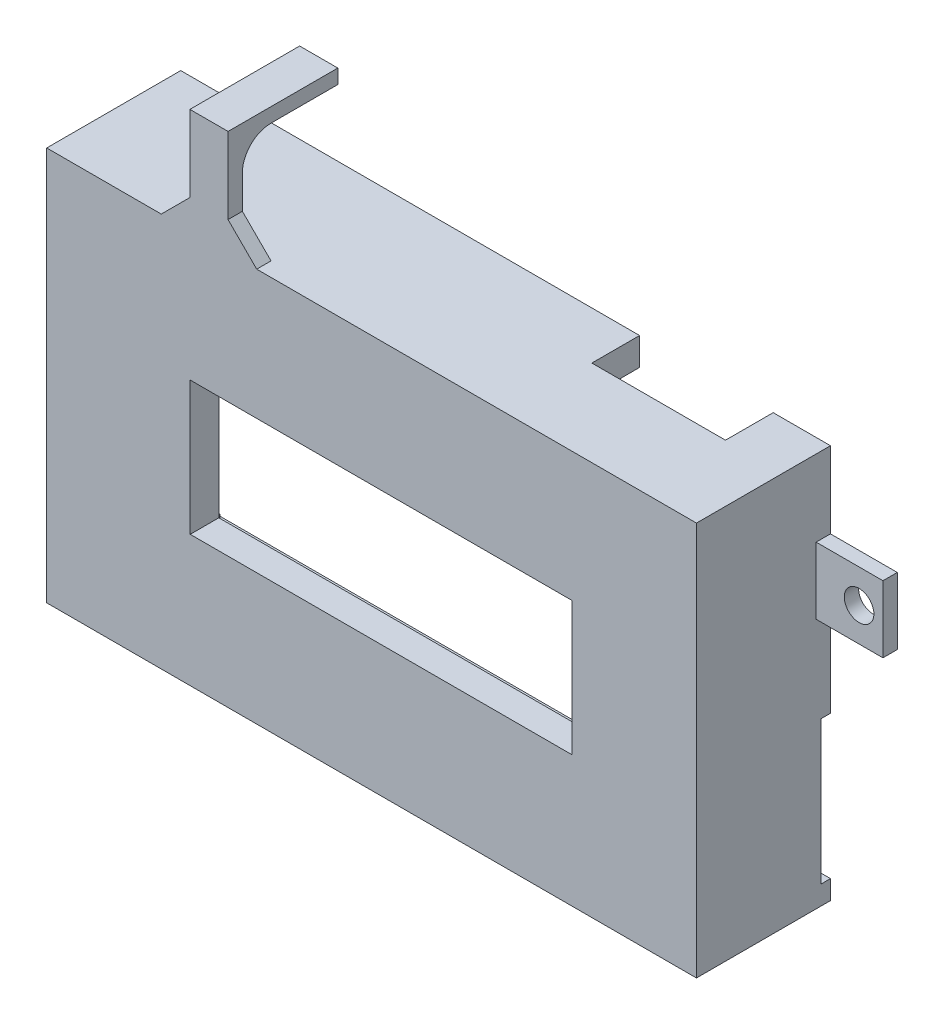
SolidWorks part; units mm, degrees
ref_plane "前视基准面" through (0, 0, 0) normal (0, 0, 1) x (1, 0, 0)
ref_plane "上视基准面" through (0, 0, 0) normal (0, 1, 0) x (1, 0, 0)
ref_plane "右视基准面" through (0, 0, 0) normal (1, 0, 0) x (0, 0, -1)
other "Configuration Table"
sketch "草图1" plane through (0, 0, 0) normal (0, 0, 1) x (1, 0, 0)
  line L0 (0, 0) -> (0, 12) construction
  line L1 (0, 0) -> (38, 0) construction
  line L2 (-1, -1) -> (39, -1)
  line L3 (-1, -1) -> (-1, 13)
  line L4 (-1, 13) -> (39, 13)
  line L5 (39, -1) -> (39, 13)
  line L6 (-16.0353, -14.7373) -> (52.0424, -14.7373)
  line L7 (-16.0353, -14.7373) -> (-16.0353, 26.5433)
  line L8 (-16.0353, 26.5433) -> (52.0424, 26.5433)
  line L9 (52.0424, -14.7373) -> (52.0424, 26.5433)
  line L10 (0, 12) -> (38, 12) construction
  line L11 (38, 0) -> (38, 12) construction
  line L12 (49.0424, 23.5433) -> (-13.0353, 23.5433) construction
  line L13 (-13.0353, 23.5433) -> (-13.0353, -11.7373) construction
  line L15 (-13.0353, -11.7373) -> (49.0424, -11.7373) construction
  line L16 (49.0424, -11.7373) -> (49.0424, 23.5433) construction
  dimension "D1" = 1
  dimension "D2" = 1
  dimension "D3" = 1
  dimension "D4" = 1
  dimension "D5" = 3
  dimension "D6" = 3
  dimension "D7" = 3
  dimension "D8" = 3
extrude "凸台-拉伸1" add sketch "草图1" against normal blind 3
sketch "草图2" plane through (0, 0, -3) normal (0, 0, -1) x (-1, 0, 0)
  line L0 (13.0353, 23.5433) -> (13.0353, -11.7373) construction
  line L1 (13.1353, 23.6433) -> (-49.5424, 23.6433)
  line L2 (13.1353, 23.6433) -> (13.1353, -11.8373)
  line L3 (13.1353, -11.8373) -> (-49.5424, -11.8373)
  line L4 (-49.5424, 23.6433) -> (-49.5424, -11.8373)
  line L5 (-49.0424, 23.5433) -> (13.0353, 23.5433) construction
  line L6 (13.0353, -11.7373) -> (-49.0424, -11.7373) construction
  line L7 (-49.0424, -11.7373) -> (-49.0424, 23.5433) construction
  line L9 (-52.0424, 26.5433) -> (16.0353, 26.5433)
  line L10 (-52.0424, 26.5433) -> (-52.0424, -14.7373)
  line L11 (-52.0424, -14.7373) -> (16.0353, -14.7373)
  line L12 (16.0353, 26.5433) -> (16.0353, -14.7373)
  dimension "D1" = 0.1
  dimension "D2" = 0.1
  dimension "D3" = 0.1
  dimension "D4" = 0.5
extrude "凸台-拉伸2" add sketch "草图2" along normal up to surface (11.0401 mm away)
sketch "草图3" plane through (-16.0353, 0, 0) normal (-1, 0, 0) x (0, 0, 1)
  line L0 (-14.0401, 26.5433) -> (-14.0401, -14.7373) construction
  line L1 (-14.0401, 0.2627) -> (-7, 0.2627)
  line L2 (-14.0401, 0.2627) -> (-14.0401, 11.5433)
  line L3 (-14.0401, 11.5433) -> (-7, 11.5433)
  line L4 (-7, 0.2627) -> (-7, 11.5433)
  line L5 (-14.0401, -14.7373) -> (0, -14.7373) construction
  line L6 (-14.0401, 26.5433) -> (0, 26.5433) construction
  line L7 (0, 26.5433) -> (0, -14.7373) construction
  dimension "D1" = 15
  dimension "D2" = 15
  dimension "D3" = 7
extrude "切除-拉伸1" cut sketch "草图3" against normal up to surface (2.9 mm away) up to face at (-13.1353, 5.903, -8.52)
sketch "草图4" plane through (0, 23.6433, 0) normal (0, -1, 0) x (1, 0, 0)
  line L0 (49.5424, -14.0401) -> (49.5424, -3) construction
  line L1 (49.5424, -12.2401) -> (46.5424, -12.2401)
  line L2 (49.5424, -12.2401) -> (49.5424, -10.4401)
  line L3 (49.5424, -10.4401) -> (46.5424, -10.4401)
  line L4 (46.5424, -12.2401) -> (46.5424, -10.4401)
  line L5 (49.5424, -14.0401) -> (-13.1353, -14.0401) construction
  dimension "D1" = 1.8
  dimension "D2" = 1.8
  dimension "D3" = 3
extrude "凸台-拉伸3" add sketch "草图4" along normal blind 3
sketch "草图5" plane through (0, -11.8373, 0) normal (0, 1, 0) x (1, 0, 0)
  line L0 (49.5424, 14.0401) -> (49.5424, 3) construction
  line L1 (49.5424, 12.2401) -> (46.5424, 12.2401)
  line L2 (49.5424, 12.2401) -> (49.5424, 10.4401)
  line L3 (49.5424, 10.4401) -> (46.5424, 10.4401)
  line L4 (46.5424, 12.2401) -> (46.5424, 10.4401)
  line L5 (-13.1353, 14.0401) -> (49.5424, 14.0401) construction
  dimension "D1" = 1.8
  dimension "D2" = 1.8
  dimension "D3" = 3
extrude "凸台-拉伸4" add sketch "草图5" along normal blind 3
sketch "草图6" plane through (0, 23.6433, 0) normal (0, -1, 0) x (1, 0, 0)
  line L0 (-13.1353, -14.0401) -> (-13.1353, -3) construction
  line L1 (-13.1353, -12.2401) -> (-10.1353, -12.2401)
  line L2 (-13.1353, -12.2401) -> (-13.1353, -10.4401)
  line L3 (-13.1353, -10.4401) -> (-10.1353, -10.4401)
  line L4 (-10.1353, -12.2401) -> (-10.1353, -10.4401)
  line L5 (49.5424, -14.0401) -> (-13.1353, -14.0401) construction
  dimension "D1" = 1.8
  dimension "D2" = 1.8
  dimension "D3" = 3
extrude "凸台-拉伸5" add sketch "草图6" along normal blind 2
sketch "草图7" plane through (0, -11.8373, 0) normal (0, 1, 0) x (1, 0, 0)
  line L1 (-13.1353, 14.0401) -> (-13.1353, 3) construction
  line L2 (-13.1353, 12.2401) -> (-10.1353, 12.2401)
  line L3 (-13.1353, 12.2401) -> (-13.1353, 10.4401)
  line L4 (-13.1353, 10.4401) -> (-10.1353, 10.4401)
  line L5 (-10.1353, 12.2401) -> (-10.1353, 10.4401)
  line L6 (-13.1353, 14.0401) -> (49.5424, 14.0401) construction
  dimension "D1" = 1.8
  dimension "D2" = 1.8
  dimension "D3" = 3
extrude "凸台-拉伸6" add sketch "草图7" along normal blind 2
sketch "草图8" plane through (0, 26.5433, 0) normal (0, 1, 0) x (1, 0, 0)
  line L0 (52.0424, 14.0401) -> (-16.0353, 14.0401) construction
  line L1 (32.0424, 14.0401) -> (46.0424, 14.0401)
  line L2 (32.0424, 14.0401) -> (32.0424, 9.0401)
  line L3 (32.0424, 9.0401) -> (46.0424, 9.0401)
  line L4 (46.0424, 14.0401) -> (46.0424, 9.0401)
  line L5 (52.0424, 14.0401) -> (52.0424, 0) construction
  dimension "D1" = 6
  dimension "D2" = 14
  dimension "D3" = 5
extrude "切除-拉伸2" cut sketch "草图8" against normal up to surface (2.9 mm away) up to face at (18.2035, 23.6433, -10.4)
sketch "草图9" plane through (52.0424, 0, 0) normal (1, 0, 0) x (0, 0, -1)
  line L1 (14.0401, -14.7373) -> (14.0401, 26.5433) construction
  line L2 (14.0401, -12.7373) -> (13.0401, -12.7373)
  line L3 (14.0401, -12.7373) -> (14.0401, 2.2627)
  line L4 (14.0401, 2.2627) -> (13.0401, 2.2627)
  line L5 (13.0401, -12.7373) -> (13.0401, 2.2627)
  line L6 (14.0401, -12.7373) -> (22.0401, -12.7373) construction
  line L7 (22.0401, 2.2627) -> (14.0401, 2.2627) construction
  dimension "D1" = 0
  dimension "D2" = 1
extrude "切除-拉伸3" cut sketch "草图9" against normal blind 1
sketch "草图10" plane through (52.0424, 0, 0) normal (1, 0, 0) x (0, 0, -1)
  line L1 (14.0401, 2.2627) -> (14.0401, 26.5433) construction
  line L2 (14.0401, 11.5433) -> (12.5401, 11.5433)
  line L3 (14.0401, 11.5433) -> (14.0401, 18.5433)
  line L4 (14.0401, 18.5433) -> (12.5401, 18.5433)
  line L5 (12.5401, 11.5433) -> (12.5401, 18.5433)
  line L6 (14.0401, 26.5433) -> (0, 26.5433) construction
  dimension "D1" = 8
  dimension "D2" = 7
  dimension "D3" = 1.5
extrude "凸台-拉伸7" add sketch "草图10" along normal blind 7
sketch "草图13" plane through (0, 0, -12.5401) normal (0, 0, 1) x (1, 0, 0)
  line L0 (59.0424, 11.5433) -> (52.0424, 11.5433) construction
  line L1 (59.0424, 18.5433) -> (59.0424, 11.5433) construction
  circle A0 centre (56.5424, 15.0433) radius 1.55
  dimension "D3" = 3.1
  dimension "D1" = 3.5
  dimension "D2" = 2.5
extrude "切除-拉伸6" cut sketch "草图13" against normal through all
sketch "草图14" plane through (0, 26.5433, 0) normal (0, 1, 0) x (1, 0, 0)
  line L0 (52.0424, 0) -> (-16.0353, 0) construction
  line L1 (2.9647, 0) -> (-1.0353, 0)
  line L2 (2.9647, 0) -> (2.9647, 1.5)
  line L3 (2.9647, 1.5) -> (-1.0353, 1.5)
  line L4 (-1.0353, 0) -> (-1.0353, 1.5)
  line L5 (-16.0353, 14.0401) -> (-16.0353, 0) construction
  dimension "D1" = 15
  dimension "D2" = 4
  dimension "D3" = 1.5
extrude "凸台-拉伸8" add sketch "草图14" along normal blind 11
sketch "草图15" plane through (0, 0, -1.5) normal (0, 0, -1) x (-1, 0, 0)
  line L0 (1.0353, 37.5433) -> (1.0353, 26.5433) construction
  line L1 (-2.9647, 37.5433) -> (1.0353, 37.5433)
  line L2 (-2.9647, 37.5433) -> (-2.9647, 36.0433)
  line L3 (-2.9647, 36.0433) -> (1.0353, 36.0433)
  line L4 (1.0353, 37.5433) -> (1.0353, 36.0433)
  dimension "D1" = 1.5
extrude "凸台-拉伸9" add sketch "草图15" along normal blind 10
chamfer "倒角1" distance 3 angle 45 2 edges at (2.9647, 26.5433, -0.75) (-1.0353, 26.5433, -0.75)
fillet "圆角2" radius 3 1 edges at (0.9647, 36.0433, -1.5)
sketch "草图16" plane through (0, -14.7373, 0) normal (0, -1, 0) x (1, 0, 0)
  line L0 (-16.0353, -14.0401) -> (52.0424, -14.0401) construction
  line L1 (13.9647, -14.0401) -> (20.9647, -14.0401)
  line L2 (13.9647, -14.0401) -> (13.9647, -12.5401)
  line L3 (13.9647, -12.5401) -> (20.9647, -12.5401)
  line L4 (20.9647, -14.0401) -> (20.9647, -12.5401)
  line L5 (-16.0353, -14.0401) -> (-16.0353, 0) construction
  point P6 (13.9647, -13.2901)
  dimension "D1" = 7
  dimension "D2" = 1.5
  dimension "D3" = 30
extrude "凸台-拉伸10" add sketch "草图16" along normal blind 7
sketch "草图17" plane through (0, 0, -12.5401) normal (0, 0, 1) x (1, 0, 0)
  line L0 (13.9647, -21.7373) -> (13.9647, -14.7373) construction
  line L1 (20.9647, -21.7373) -> (13.9647, -21.7373) construction
  circle A0 centre (17.4647, -19.2373) radius 1.55
  dimension "D3" = 3.1
  dimension "D1" = 3.5
  dimension "D2" = 2.5
extrude "切除-拉伸7" cut sketch "草图17" against normal through all contours A0
